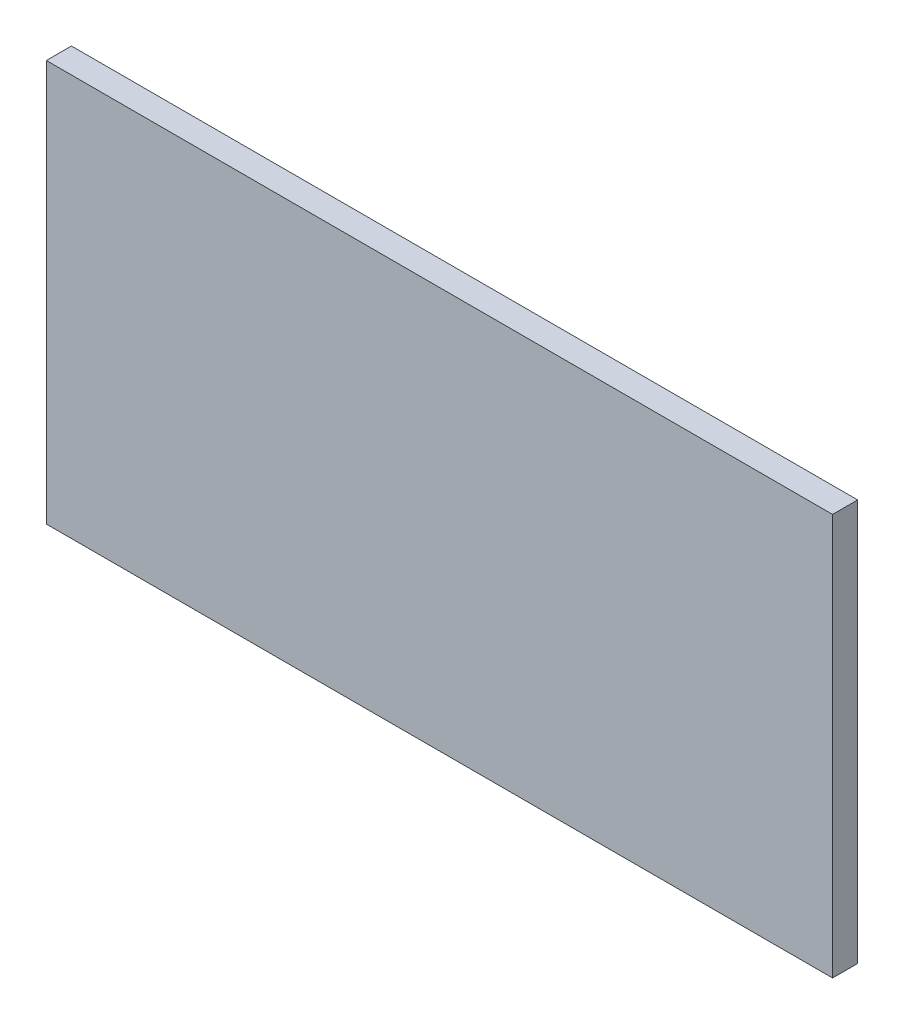
SolidWorks part; units mm, degrees
ref_plane "Front Plane" through (0, 0, 0) normal (0, 0, 1) x (1, 0, 0)
ref_plane "Top Plane" through (0, 0, 0) normal (0, 1, 0) x (1, 0, 0)
ref_plane "Right Plane" through (0, 0, 0) normal (1, 0, 0) x (0, 0, -1)
sketch "Sketch1" plane through (0, 0, 0) normal (0, 0, 1) x (1, 0, 0)
  line L1 (282, -144) -> (-282, -144)
  line L2 (282, -144) -> (282, 144)
  line L3 (282, 144) -> (-282, 144)
  line L4 (-282, -144) -> (-282, 144)
  line L5 (282, -144) -> (-282, 144) construction
  line L6 (282, 144) -> (-282, -144) construction
  point P0 (0, 0)
  dimension "D1" = 288
  dimension "D2" = 564
extrude "Boss-Extrude1" add sketch "Sketch1" along normal blind 18
equation "\"H_DSP\"=18"
equation "\"D1@Boss-Extrude1\"=\"H_DSP\""
